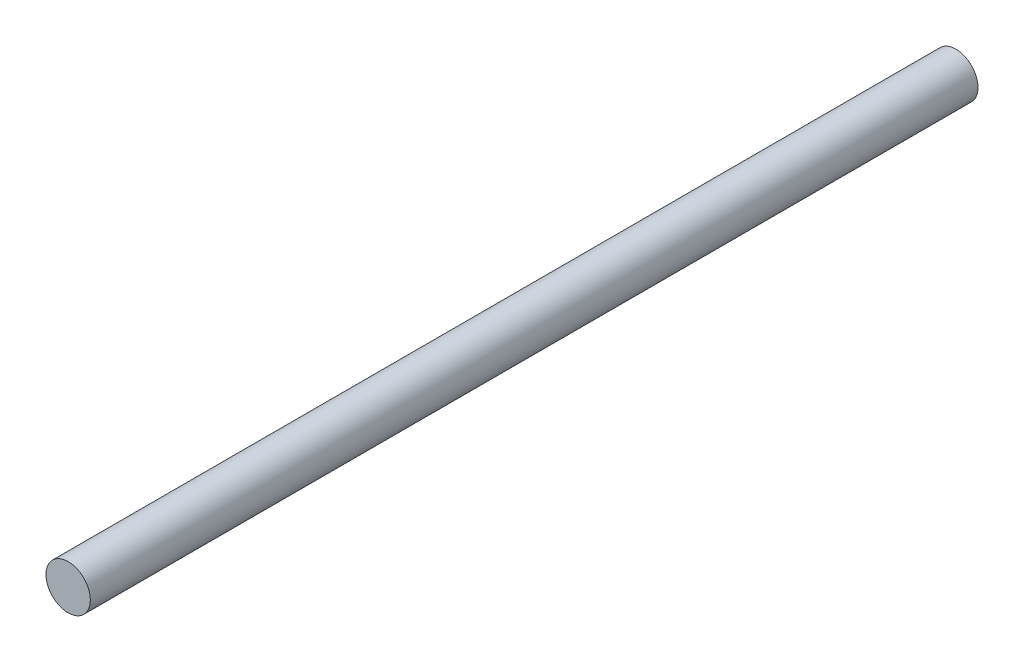
SolidWorks part; units mm, degrees
ref_plane "Plan de face" through (0, 0, 0) normal (0, 0, 1) x (1, 0, 0)
ref_plane "Plan de dessus" through (0, 0, 0) normal (0, 1, 0) x (1, 0, 0)
ref_plane "Plan de droite" through (0, 0, 0) normal (1, 0, 0) x (0, 0, -1)
sketch "Esquisse1" plane through (0, 0, 0) normal (0, 0, 1) x (1, 0, 0)
  circle A0 centre (0, 0) radius 1
  dimension "D1" = 2
extrude "Boss.-Extru.1" add sketch "Esquisse1" against normal blind 40
